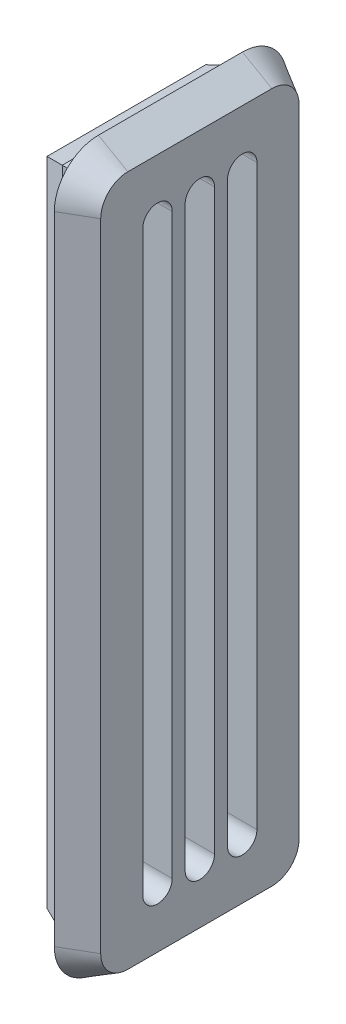
SolidWorks part; units mm, degrees
ref_plane "前视基准面" through (0, 0, 0) normal (0, 0, 1) x (1, 0, 0)
ref_plane "上视基准面" through (0, 0, 0) normal (0, 1, 0) x (1, 0, 0)
ref_plane "右视基准面" through (0, 0, 0) normal (1, 0, 0) x (0, 0, -1)
other "Configuration Table"
sketch "草图1" plane through (0, 0, 0) normal (1, 0, 0) x (0, 0, -1)
  line L0 (-147.2592, 67.5612) -> (-135.4592, 67.5612)
  line L1 (-147.3592, 67.6612) -> (-135.3592, 67.6612) construction
  line L2 (-147.3592, 67.6612) -> (-147.3592, 22.1612) construction
  line L3 (-147.3592, 22.1612) -> (-135.3592, 22.1612) construction
  line L4 (-135.3592, 67.6612) -> (-135.3592, 22.1612) construction
  line L5 (-135.4592, 67.5612) -> (-135.4592, 22.2612)
  line L6 (-147.2592, 22.2612) -> (-135.4592, 22.2612)
  line L7 (-147.2592, 67.5612) -> (-147.2592, 22.2612)
  line L8 (-145.7592, 66.0612) -> (-145.7592, 23.7612)
  line L9 (-145.7592, 23.7612) -> (-136.9592, 23.7612)
  line L10 (-136.9592, 66.0612) -> (-136.9592, 23.7612)
  line L11 (-145.7592, 66.0612) -> (-136.9592, 66.0612)
  dimension "D1" = 12
  dimension "D2" = 45.5
  dimension "D3" = 0.1
  dimension "D4" = 1.5
extrude "凸台-拉伸1" add sketch "草图1" along normal blind 3
sketch "草图2" plane through (3, 0, 0) normal (1, 0, 0) x (0, 0, -1)
  line L12 (-149.2592, 20.2612) -> (-133.4592, 20.2612)
  line L13 (-149.2592, 69.5612) -> (-149.2592, 20.2612)
  line L14 (-133.4592, 69.5612) -> (-149.2592, 69.5612)
  line L15 (-133.4592, 20.2612) -> (-133.4592, 69.5612)
  line L16 (-146.2592, 20.2612) -> (-136.4592, 20.2612)
  line L17 (-149.2592, 66.5612) -> (-149.2592, 23.2612)
  line L18 (-136.4592, 69.5612) -> (-146.2592, 69.5612)
  line L19 (-133.4592, 23.2612) -> (-133.4592, 66.5612)
  arc A0 (-136.4592, 69.5612) -> (-133.4592, 66.5612) centre (-136.4592, 66.5612) cw
  arc A1 (-136.4592, 20.2612) -> (-133.4592, 23.2612) centre (-136.4592, 23.2612) ccw
  arc A2 (-146.2592, 20.2612) -> (-149.2592, 23.2612) centre (-146.2592, 23.2612) cw
  arc A3 (-149.2592, 66.5612) -> (-146.2592, 69.5612) centre (-146.2592, 66.5612) cw
  dimension "D2" = 3
  dimension "D1" = 2
extrude "凸台-拉伸2" add sketch "草图2" along normal blind 2 draft 30
sketch "草图3" plane through (3, 0, 0) normal (-1, 0, 0) x (0, 0, 1)
  line L0 (136.4592, 69.5612) -> (146.2592, 69.5612) construction
  line L1 (144.2415, 64.5612) -> (144.2415, 25.2612) construction
  line L2 (145.2415, 64.5612) -> (145.2415, 25.2612)
  line L3 (143.2415, 64.5612) -> (143.2415, 25.2612)
  line L4 (146.2592, 20.2612) -> (136.4592, 20.2612) construction
  line L5 (141.3592, 64.5612) -> (141.3592, 25.2612) construction
  line L6 (142.3592, 64.5612) -> (142.3592, 25.2612)
  line L7 (140.3592, 64.5612) -> (140.3592, 25.2612)
  line L8 (138.4769, 64.5612) -> (138.4769, 25.2612) construction
  line L9 (139.4769, 64.5612) -> (139.4769, 25.2612)
  line L10 (137.4769, 64.5612) -> (137.4769, 25.2612)
  line L11 (145.7592, 23.7612) -> (136.9592, 23.7612) construction
  arc A43 (145.2415, 64.5612) -> (143.2415, 64.5612) centre (144.2415, 64.5612) ccw
  arc A44 (143.2415, 25.2612) -> (145.2415, 25.2612) centre (144.2415, 25.2612) ccw
  arc A45 (142.3592, 64.5612) -> (140.3592, 64.5612) centre (141.3592, 64.5612) ccw
  arc A46 (140.3592, 25.2612) -> (142.3592, 25.2612) centre (141.3592, 25.2612) ccw
  arc A47 (139.4769, 64.5612) -> (137.4769, 64.5612) centre (138.4769, 64.5612) ccw
  arc A48 (137.4769, 25.2612) -> (139.4769, 25.2612) centre (138.4769, 25.2612) ccw
  point P5 (144.2415, 44.9112)
  point P12 (0, 0)
  point P15 (141.3592, 44.9112)
  point P22 (138.4769, 44.9112)
  point P29 (141.3592, 23.7612)
  dimension "D1" = 5
  dimension "D3" = 1
  dimension "D2" = 5
  dimension "D4" = 3
extrude "切除-拉伸1" cut sketch "草图3" against normal up to next
chamfer "倒角1" distance 0.5 angle 72 4 edges at (0, 67.5612, 141.3592) (0, 44.9112, 135.4592) (0, 22.2612, 141.3592) (0, 44.9112, 147.2592)
